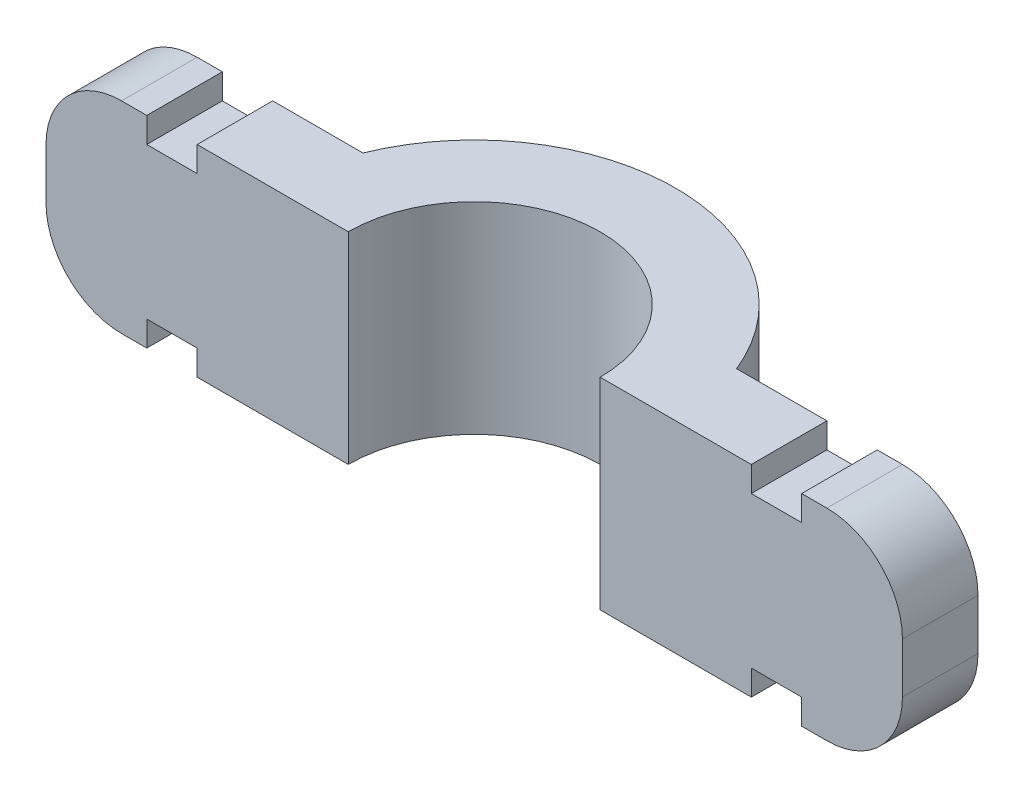
SolidWorks part; units mm, degrees
ref_plane "前基準面" through (0, 0, 0) normal (0, 0, 1) x (1, 0, 0)
ref_plane "上基準面" through (0, 0, 0) normal (0, 1, 0) x (1, 0, 0)
ref_plane "右基準面" through (0, 0, 0) normal (1, 0, 0) x (0, 0, -1)
sketch "草圖1" plane through (0, 0, 0) normal (0, 1, 0) x (1, 0, 0)
  line L0 (-12, 13.3037) -> (-12, -19.2583) construction
  line L1 (-5, 0) -> (-17, 0)
  line L2 (-17, 0) -> (-17, 3)
  line L3 (-17, 3) -> (-7.4162, 3)
  line L4 (0, 3.3006) -> (0, -12.5725) construction
  line L5 (17, 0) -> (17, 3)
  line L6 (5, 0) -> (17, 0)
  line L7 (17, 3) -> (7.4162, 3)
  arc A0 (5, 0) -> (-5, 0) centre (0, 0) ccw
  arc A1 (7.4162, 3) -> (-7.4162, 3) centre (0, 0) ccw
  dimension "D1" = 5
  dimension "D2" = 8
  dimension "D3" = 12
  dimension "D4" = 12
  dimension "D5" = 3
extrude "填料-伸長1" add sketch "草圖1" along normal mid plane 8
sketch "草圖2" plane through (0, 4, 0) normal (0, 1, 0) x (1, 0, 0)
  line L0 (-12, 7.6827) -> (-12, -8.4422) construction
  line L1 (0, 9.2694) -> (0, -8.4422) construction
  line L2 (-7.4162, 3) -> (-17, 3) construction
  line L3 (-17, 0) -> (-5, 0) construction
  line L4 (-13, 3) -> (-11, 3)
  line L5 (-13, 3) -> (-13, 0)
  line L6 (-13, 0) -> (-11, 0)
  line L7 (-11, 3) -> (-11, 0)
  line L8 (11, 3) -> (11, 0)
  line L9 (13, 0) -> (11, 0)
  line L10 (13, 3) -> (13, 0)
  line L11 (13, 3) -> (11, 3)
  point P13 (0, 0)
  dimension "D1" = 12
extrude "除料-伸長1" cut sketch "草圖2" against normal blind 1
mirror "鏡射1" about plane through (0, 0, 0) normal (0, 1, 0) of "除料-伸長1"
fillet "圓角1" radius 3 4 edges at (17, -4, -1.5) (17, 4, -1.5) (-17, -4, -1.5) (-17, 4, -1.5)
